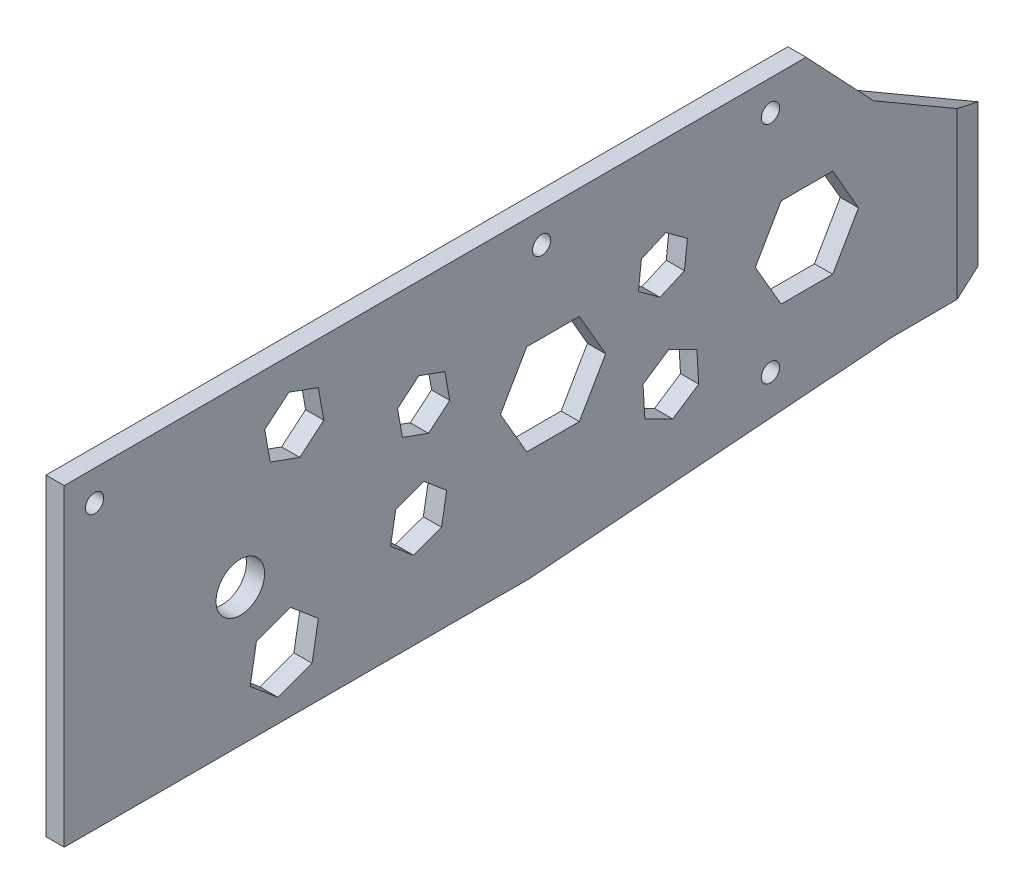
SolidWorks part; units mm, degrees
ref_plane "Alzado" through (0, 0, 0) normal (0, 0, 1) x (1, 0, 0)
ref_plane "Planta" through (0, 0, 0) normal (0, 1, 0) x (1, 0, 0)
ref_plane "Vista lateral" through (0, 0, 0) normal (1, 0, 0) x (0, 0, -1)
sketch "Croquis1" plane through (0, 0, 0) normal (1, 0, 0) x (0, 0, -1)
  line L1 (-80.5, -25.7906) -> (80.5, -25.7906)
  line L2 (-80.5, -25.7906) -> (-80.5, 25.7906)
  line L3 (-80.5, 25.7906) -> (80.5, 25.7906)
  line L4 (80.5, -25.7906) -> (80.5, 25.7906)
  line L5 (-80.5, -25.7906) -> (80.5, 25.7906) construction
  line L6 (-80.5, 25.7906) -> (80.5, -25.7906) construction
  point P0 (0, 0)
  dimension "D1" = 51.5812
  dimension "D2" = 161
extrude "Saliente-Extruir1" add sketch "Croquis1" along normal blind 3
sketch "Croquis2" plane through (3, 0, 0) normal (1, 0, 0) x (0, 0, -1)
  line L0 (-80.5, 25.7906) -> (-75.5, 25.7906) construction
  line L1 (80.5, 25.7906) -> (-80.5, 25.7906) construction
  line L2 (-75.5, 25.7906) -> (-75.5, 20.7906) construction
  line L3 (-75.5, 20.7906) -> (-75.5, -8.2094) construction
  line L4 (-75.5, 20.7906) -> (-51.5, 20.7906) construction
  line L5 (-51.5, 20.7906) -> (-51.5, -3.2094) construction
  circle A0 centre (-75.5, 20.7906) radius 1.5
  circle A1 centre (-1.88, 20.7906) radius 1.5
  circle A2 centre (-51.5, -3.2094) radius 4
  dimension "D1" = 3
  dimension "D4" = 3
  dimension "D5" = 8
  dimension "D2" = 5
  dimension "D3" = 5
extrude "Cortar-Extruir1" cut sketch "Croquis2" against normal up to next
sketch "Croquis3" plane through (0, 0, 0) normal (-1, 0, 0) x (0, 0, 1)
  circle A0 centre (-35.8015, -16.2094) radius 1.5
extrude "Cortar-Extruir2" cut sketch "Croquis3" against normal up to next
sketch "Croquis4" plane through (0, 25.7906, 0) normal (0, 1, 0) x (1, 0, 0)
  line L0 (3, 80.5) -> (0, 80.5)
  line L1 (0, 80.5) -> (0, 72.9804)
  line L2 (0, 80.5) -> (0, -80.5) construction
  line L3 (-6.3093, 86.5109) -> (5.9121, 60.3018) construction
  line L4 (0, 72.9804) -> (3, 66.5469)
  line L5 (3, 80.5) -> (3, -80.5) construction
  line L6 (3, 66.5469) -> (3, 80.5)
extrude "Cortar-Extruir3" cut sketch "Croquis4" against normal up to next
sketch "Croquis5" plane through (0, 0, 0) normal (-1, 0, 0) x (0, 0, 1)
  line L0 (-72.9804, -25.7906) -> (-72.9804, -21.1495)
  line L1 (-72.9804, -25.7906) -> (-72.9804, 25.7906) construction
  line L2 (-72.9804, -21.1495) -> (-55.5955, -21.2094)
  line L3 (-55.5955, -21.2094) -> (3.7598, -25.7906)
  line L4 (80.5, -25.7906) -> (-72.9804, -25.7906) construction
  line L5 (3.7598, -25.7906) -> (-72.9804, -25.7906)
extrude "Cortar-Extruir4" cut sketch "Croquis5" against normal up to next
sketch "Croquis6" plane through (0, 0, 0) normal (-1, 0, 0) x (0, 0, 1)
  line L0 (-72.9804, 25.7906) -> (-72.9804, 2.2906)
  line L1 (-72.9804, -21.1495) -> (-72.9804, 25.7906) construction
  line L2 (-72.9804, 25.7906) -> (-52.7704, 25.7906)
  line L3 (-72.9804, 25.7906) -> (80.5, 25.7906) construction
  line L4 (-52.7704, 25.7906) -> (-52.7704, 14.0406)
  line L5 (-52.7704, 14.0406) -> (-72.9804, 2.2906)
extrude "Cortar-Extruir5" cut sketch "Croquis6" against normal up to next
sketch "Croquis7" plane through (0, 0, 0) normal (-1, 0, 0) x (0, 0, 1)
  line L0 (-52.7704, 25.7906) -> (-41.6704, 25.7906)
  line L1 (-52.7704, 25.7906) -> (80.5, 25.7906) construction
  line L2 (-52.7704, 25.7906) -> (-52.7704, 14.0406)
  line L3 (-52.7704, 14.0406) -> (-52.7704, 25.7906) construction
  line L4 (-52.7704, 14.0406) -> (-41.6704, 25.7906)
extrude "Cortar-Extruir6" cut sketch "Croquis7" against normal up to next
sketch "Croquis8" plane through (0, 0, 0) normal (-1, 0, 0) x (0, 0, 1)
  line L0 (0, 0) -> (-58.2534, 0) construction
  line L1 (0, 0) -> (43.8268, 0) construction
  line L2 (0, 0) -> (42.6107, 15.509) construction
  line L3 (0, 0) -> (44.2658, -16.1114) construction
  line L4 (0, 0) -> (-36.1868, 15.927) construction
  line L5 (0, 0) -> (-38.8052, -19.3888) construction
  line L7 (8.6603, 0) -> (4.3301, 7.5)
  line L8 (4.3301, 7.5) -> (-4.3301, 7.5)
  line L9 (-4.3301, 7.5) -> (-8.6603, 0)
  line L10 (-8.6603, 0) -> (-4.3301, -7.5)
  line L11 (-4.3301, -7.5) -> (4.3301, -7.5)
  line L12 (4.3301, -7.5) -> (8.6603, 0)
  line L13 (25.6042, 9.3192) -> (22.0997, 12.2597)
  line L14 (22.0997, 12.2597) -> (17.8009, 10.6951)
  line L15 (17.8009, 10.6951) -> (17.0065, 6.1899)
  line L16 (17.0065, 6.1899) -> (20.5109, 3.2493)
  line L17 (20.5109, 3.2493) -> (24.8098, 4.8139)
  line L18 (24.8098, 4.8139) -> (25.6042, 9.3192)
  line L19 (-23.9887, -11.9858) -> (-19.7112, -14.8118)
  line L20 (-19.7112, -14.8118) -> (-15.1251, -12.5204)
  line L21 (-15.1251, -12.5204) -> (-14.8165, -7.403)
  line L22 (-14.8165, -7.403) -> (-19.094, -4.577)
  line L23 (-19.094, -4.577) -> (-23.6801, -6.8684)
  line L24 (-23.6801, -6.8684) -> (-23.9887, -11.9858)
  line L25 (-22.1232, 9.7372) -> (-21.6444, 5.3604)
  line L26 (-21.6444, 5.3604) -> (-17.6145, 3.5868)
  line L27 (-17.6145, 3.5868) -> (-14.0636, 6.1899)
  line L28 (-14.0636, 6.1899) -> (-14.5425, 10.5666)
  line L29 (-14.5425, 10.5666) -> (-18.5723, 12.3403)
  line L30 (-18.5723, 12.3403) -> (-22.1232, 9.7372)
  line L31 (26.7527, -9.7372) -> (25.899, -4.8956)
  line L32 (25.899, -4.8956) -> (21.2792, -3.2141)
  line L33 (21.2792, -3.2141) -> (17.5131, -6.3742)
  line L34 (17.5131, -6.3742) -> (18.3668, -11.2159)
  line L35 (18.3668, -11.2159) -> (22.9866, -12.8973)
  line L36 (22.9866, -12.8973) -> (26.7527, -9.7372)
  line L37 (-50.3008, 0) -> (-46.053, -7.3574)
  line L38 (-46.053, -7.3574) -> (-37.5574, -7.3574)
  line L39 (-37.5574, -7.3574) -> (-33.3096, 0)
  line L40 (-33.3096, 0) -> (-37.5574, 7.3574)
  line L41 (-37.5574, 7.3574) -> (-46.053, 7.3574)
  line L42 (-46.053, 7.3574) -> (-50.3008, 0)
  line L43 (37.7467, 13.7387) -> (41.7118, 10.4115)
  line L44 (41.7118, 10.4115) -> (46.5758, 12.1819)
  line L45 (46.5758, 12.1819) -> (47.4746, 17.2794)
  line L46 (47.4746, 17.2794) -> (43.5095, 20.6065)
  line L47 (43.5095, 20.6065) -> (38.6455, 18.8362)
  line L48 (38.6455, 18.8362) -> (37.7467, 13.7387)
  line L49 (38.6455, -14.0658) -> (39.6841, -19.9559)
  line L50 (39.6841, -19.9559) -> (45.3044, -22.0015)
  line L51 (45.3044, -22.0015) -> (49.886, -18.157)
  line L52 (49.886, -18.157) -> (48.8475, -12.2669)
  line L53 (48.8475, -12.2669) -> (43.2272, -10.2213)
  line L54 (43.2272, -10.2213) -> (38.6455, -14.0658)
  circle A0 centre (0, 0) radius 7.5 construction
  circle A1 centre (21.3053, 7.7545) radius 3.9618 construction
  circle A2 centre (-19.4026, -9.6944) radius 4.4399 construction
  circle A3 centre (-18.0934, 7.9635) radius 3.813 construction
  circle A4 centre (22.1329, -8.0557) radius 4.2576 construction
  circle A5 centre (-41.8052, 0) radius 7.3574 construction
  circle A6 centre (42.6107, 15.509) radius 4.4827 construction
  circle A7 centre (44.2658, -16.1114) radius 5.1797 construction
  dimension "D1" = 20
  dimension "D2" = 20
extrude "Cortar-Extruir7" cut sketch "Croquis8" against normal up to next
sketch "Croquis9" plane through (0, 0, 0) normal (-1, 0, 0) x (0, 0, 1)
  line L0 (-35.8015, -16.2094) -> (-35.8015, 25.7906) construction
  line L1 (-41.6704, 25.7906) -> (80.5, 25.7906) construction
  line L2 (1.8763, 20.7906) -> (-35.8015, 20.7906) construction
  circle A1 centre (-35.8015, 20.7906) radius 1.5
  dimension "D1" = 3
extrude "Cortar-Extruir8" cut sketch "Croquis9" against normal up to next
